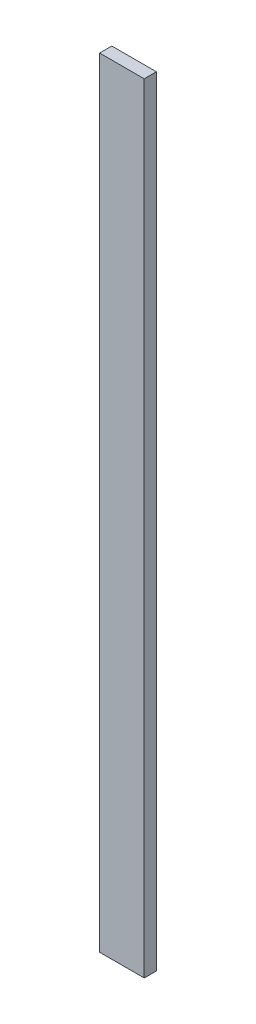
SolidWorks part; units mm, degrees
material "Oak"
ref_plane "Front Plane" through (0, 0, 0) normal (0, 0, 1) x (1, 0, 0)
ref_plane "Top Plane" through (0, 0, 0) normal (0, 1, 0) x (1, 0, 0)
ref_plane "Right Plane" through (0, 0, 0) normal (1, 0, 0) x (0, 0, -1)
sketch "Sketch1" plane through (0, 0, 0) normal (0, 1, 0) x (1, 0, 0)
  line L1 (-69.85, -19.05) -> (69.85, -19.05)
  line L2 (-69.85, -19.05) -> (-69.85, 19.05)
  line L3 (-69.85, 19.05) -> (69.85, 19.05)
  line L4 (69.85, -19.05) -> (69.85, 19.05)
  line L5 (-69.85, -19.05) -> (69.85, 19.05) construction
  line L6 (-69.85, 19.05) -> (69.85, -19.05) construction
  point P0 (0, 0)
  dimension "D1" = 38.1
  dimension "D2" = 139.7
extrude "Boss-Extrude1" add sketch "Sketch1" along normal blind 2438.4 contours L1 L4 L3 L2
